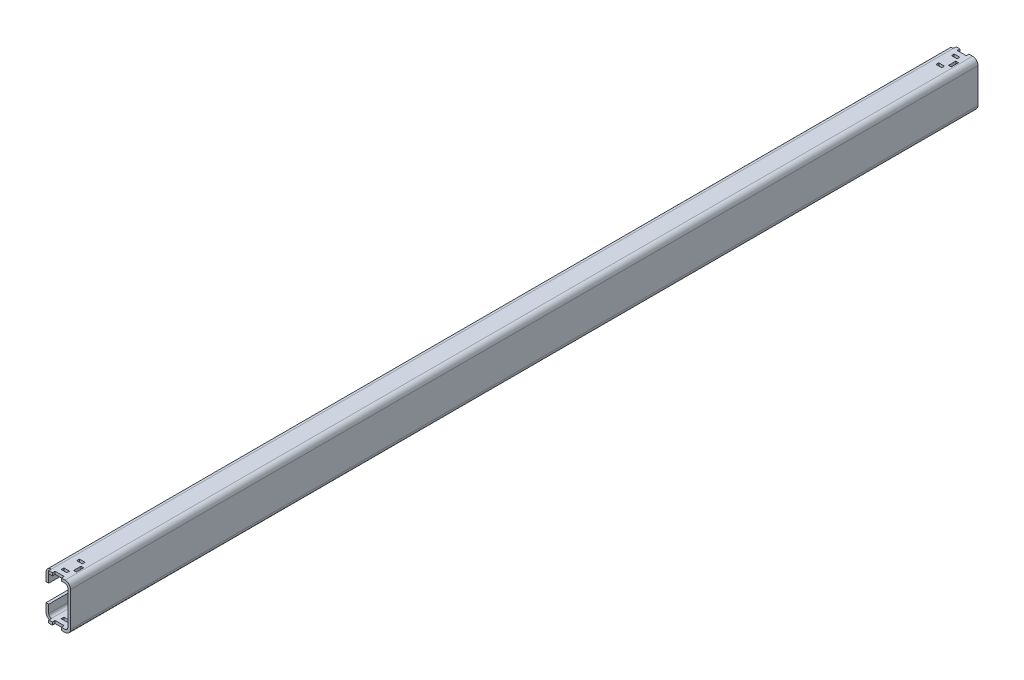
SolidWorks part; units mm, degrees
ref_plane "Front Plane" through (0, 0, 0) normal (0, 0, 1) x (1, 0, 0)
ref_plane "Top Plane" through (0, 0, 0) normal (0, 1, 0) x (1, 0, 0)
ref_plane "Right Plane" through (0, 0, 0) normal (1, 0, 0) x (0, 0, -1)
sketch "Sketch1" plane through (0, 0, 0) normal (0, 0, 1) x (1, 0, 0)
  line L0 (0, 0) -> (30, 0)
  line L1 (30, 0) -> (30, 50)
  line L2 (30, 50) -> (0, 50)
  line L6 (0, 50) -> (0, 35)
  line L7 (0, 15) -> (0, 0)
  line L8 (3, 15) -> (3, 3)
  line L9 (3, 3) -> (27, 3)
  line L10 (27, 3) -> (27, 47)
  line L11 (27, 47) -> (3, 47)
  line L12 (3, 47) -> (3, 35)
  line L13 (0, 35) -> (3, 35)
  line L14 (3, 15) -> (0, 15)
  dimension "D1" = 30
  dimension "D2" = 50
  dimension "D3" = 15
  dimension "D5" = 3
extrude "Boss-Extrude1" add sketch "Sketch1" along normal mid plane 1000
fillet "Fillet1" radius 6 4 edges at (30, 0, 0) (30, 50, 0) (0, 0, 0) (0, 50, 0)
fillet "Fillet2" radius 3 4 edges at (27, 47, 0) (3, 47, 0) (3, 3, 0) (27, 3, 0)
sketch "Sketch2" plane through (0, 50, 0) normal (0, 1, 0) x (1, 0, 0)
  line L0 (24, 500) -> (6, 500) construction
  line L1 (10, 500) -> (20, 500)
  line L2 (10, 500) -> (10, 497)
  line L3 (10, 497) -> (20, 497)
  line L4 (20, 500) -> (20, 497)
  line L5 (0, 0) -> (159.7054, 0) construction
  line L10 (0, -500) -> (0, 500) construction
  line L11 (6, 500) -> (0, 500)
  line L12 (6, 500) -> (6, 497)
  line L13 (6, 497) -> (0, 497)
  line L14 (0, 500) -> (0, 497)
  line L15 (0, -500) -> (0, -497)
  line L16 (6, -497) -> (0, -497)
  line L17 (6, -500) -> (6, -497)
  line L18 (6, -500) -> (0, -500)
  line L19 (20, -500) -> (20, -497)
  line L20 (10, -497) -> (20, -497)
  line L21 (10, -500) -> (10, -497)
  line L22 (10, -500) -> (20, -500)
  line L23 (24, -500) -> (24, 500) construction
  line L24 (11.7586, 492) -> (17.9604, 492)
  line L26 (11.7586, 472) -> (17.9604, 472)
  line L27 (22.5, 486) -> (22.5, 478)
  line L29 (11.7586, 489) -> (17.9604, 489)
  line L30 (19.5, 486) -> (19.5, 478)
  line L31 (11.7586, 475) -> (17.9604, 475)
  line L33 (11.7586, 489) -> (11.7586, 492)
  line L34 (17.9604, 489) -> (17.9604, 492)
  line L35 (19.5, 486) -> (22.5, 486)
  line L36 (19.5, 478) -> (22.5, 478)
  line L37 (17.9604, 475) -> (17.9604, 472)
  line L38 (11.7586, 475) -> (11.7586, 472)
  line L39 (7.5, 492) -> (22.5, 492) construction
  line L40 (10.5, 489) -> (10.5, 475) construction
  line L41 (7.5, 492) -> (7.5, 472) construction
  line L42 (10.5, 489) -> (19.5, 489) construction
  line L43 (10.5, 475) -> (19.5, 475) construction
  line L44 (7.5, 472) -> (22.5, 472) construction
  line L45 (22.5, 492) -> (22.5, 472) construction
  line L46 (19.5, 489) -> (19.5, 475) construction
  line L47 (11.7586, -475) -> (11.7586, -472)
  line L48 (11.7586, -472) -> (17.9604, -472)
  line L49 (17.9604, -475) -> (17.9604, -472)
  line L50 (11.7586, -475) -> (17.9604, -475)
  line L51 (19.5, -486) -> (22.5, -486)
  line L52 (19.5, -486) -> (19.5, -478)
  line L53 (19.5, -478) -> (22.5, -478)
  line L54 (22.5, -486) -> (22.5, -478)
  line L55 (11.7586, -489) -> (11.7586, -492)
  line L56 (11.7586, -489) -> (17.9604, -489)
  line L57 (17.9604, -489) -> (17.9604, -492)
  line L58 (11.7586, -492) -> (17.9604, -492)
  dimension "D1" = 3
  dimension "D2" = 10
  dimension "D3" = 10
  dimension "D4" = 20
  dimension "D5" = 6.2018
  dimension "D6" = 8
  dimension "D7" = 1.5
  dimension "D8" = 3
  dimension "D9" = 4.5396
  dimension "D10" = 8
  dimension "D11" = 3
extrude "Cut-Extrude1" cut sketch "Sketch2" against normal up to surface (50 mm away) up to face at (15, 0, 0)
